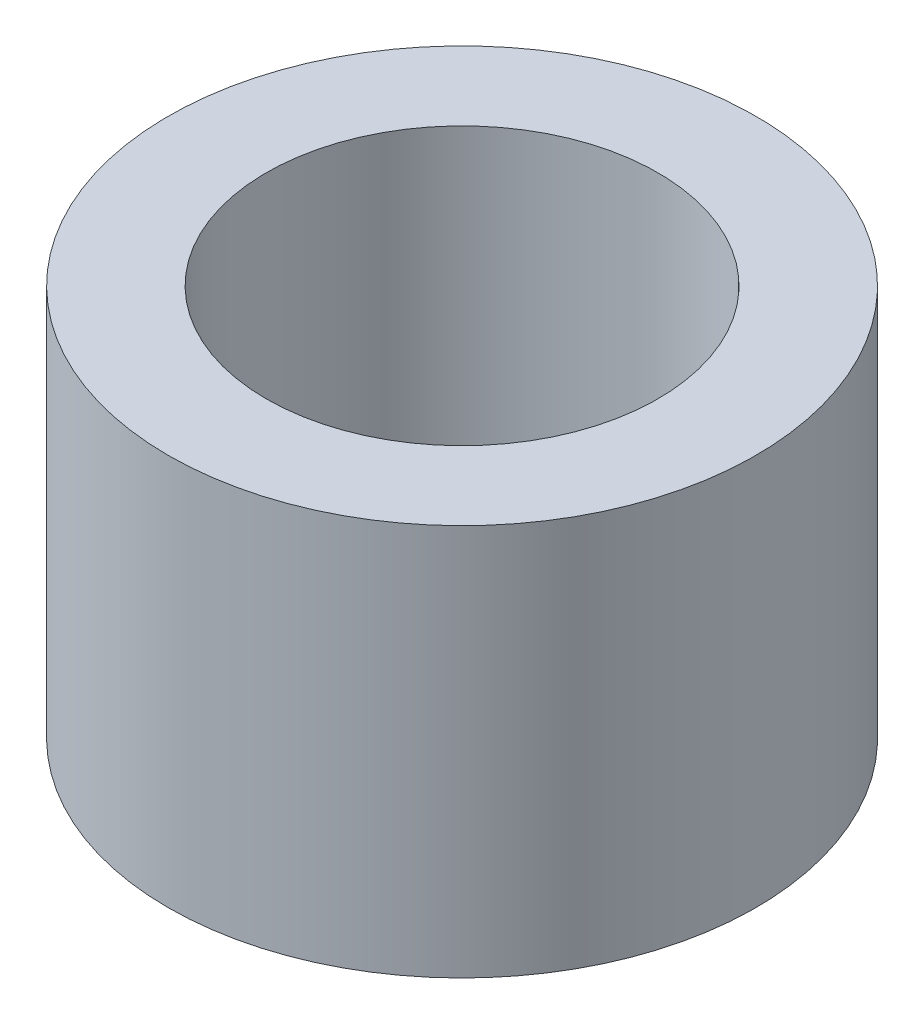
SolidWorks part; units mm, degrees
ref_plane "Front" through (0, 0, 0) normal (0, 0, 1) x (1, 0, 0)
ref_plane "Top" through (0, 0, 0) normal (0, 1, 0) x (1, 0, 0)
ref_plane "Right" through (0, 0, 0) normal (1, 0, 0) x (0, 0, -1)
sketch "Sketch1" plane through (0, 0, 0) normal (0, 1, 0) x (1, 0, 0)
  circle A0 centre (-10.609, -4.8913) radius 9.525
  circle A1 centre (-10.609, -4.8913) radius 6.35
  dimension "D1" = 12.7
  dimension "D2" = 19.05
extrude "Boss-Extrude1" add sketch "Sketch1" along normal blind 12.7
